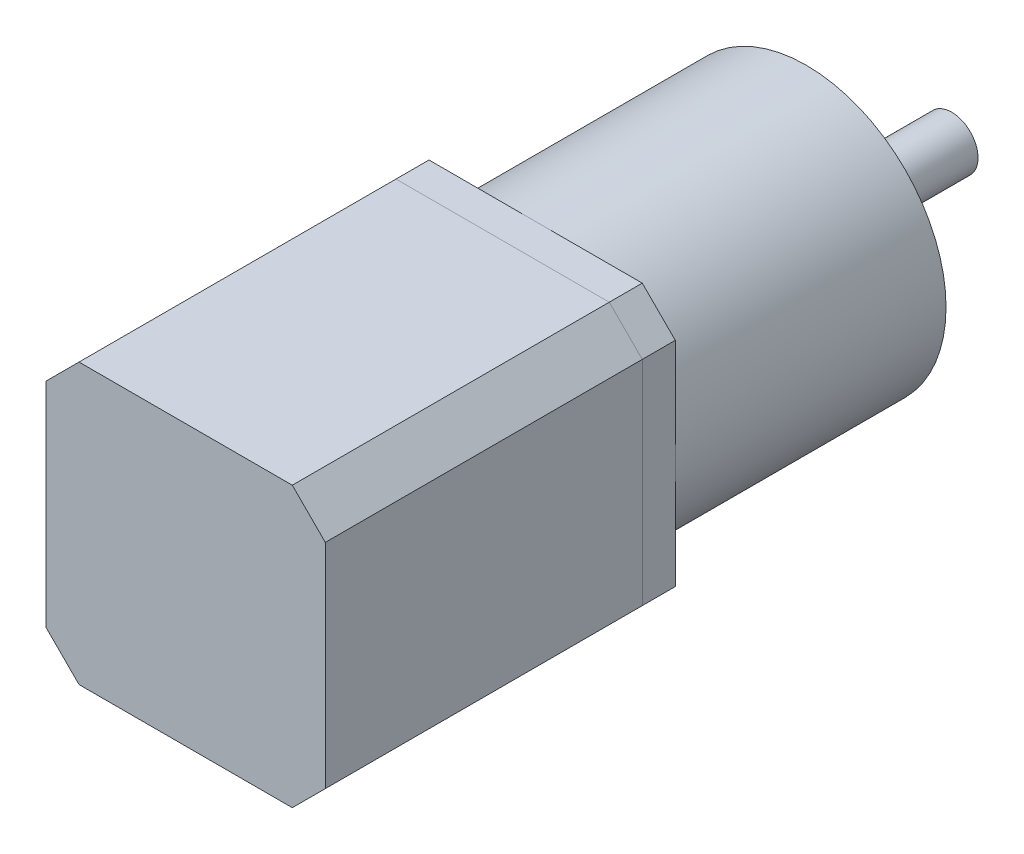
SolidWorks part; units mm, degrees
ref_plane "Front Plane" through (0, 0, 0) normal (0, 0, 1) x (1, 0, 0)
ref_plane "Top Plane" through (0, 0, 0) normal (0, 1, 0) x (1, 0, 0)
ref_plane "Right Plane" through (0, 0, 0) normal (1, 0, 0) x (0, 0, -1)
sketch "Sketch1" plane through (0, 0, 0) normal (0, 0, 1) x (1, 0, 0)
  line L1 (-21.15, 21.15) -> (21.15, 21.15)
  line L2 (-21.15, 21.15) -> (-21.15, -21.15)
  line L3 (-21.15, -21.15) -> (21.15, -21.15)
  line L4 (21.15, 21.15) -> (21.15, -21.15)
  line L5 (-21.15, 21.15) -> (21.15, -21.15) construction
  line L6 (-21.15, -21.15) -> (21.15, 21.15) construction
  point P0 (0, 0)
  dimension "D1" = 42.3
  dimension "D2" = 42.3
extrude "Boss-Extrude1" add sketch "Sketch1" along normal blind 48
chamfer "Chamfer1" distance 5 angle 45 4 edges at (-21.15, -21.15, 24) (21.15, -21.15, 24) (-21.15, 21.15, 24) (21.15, 21.15, 24)
sketch "Sketch2" plane through (0, 0, 0) normal (0, 0, -1) x (-1, 0, 0)
  line L1 (-21.15, -21.15) -> (21.15, -21.15)
  line L2 (-21.15, -21.15) -> (-21.15, 21.15)
  line L3 (-21.15, 21.15) -> (21.15, 21.15)
  line L4 (21.15, -21.15) -> (21.15, 21.15)
  line L5 (-21.15, -21.15) -> (21.15, 21.15) construction
  line L6 (-21.15, 21.15) -> (21.15, -21.15) construction
  point P0 (0, 0)
  dimension "D1" = 42.3
  dimension "D2" = 42.3
extrude "Boss-Extrude2" add sketch "Sketch2" along normal blind 5 separate body
chamfer "Chamfer2" distance 5 angle 45 4 edges at (21.15, -21.15, -2.5) (-21.15, -21.15, -2.5) (21.15, 21.15, -2.5) (-21.15, 21.15, -2.5)
sketch "Sketch3" plane through (0, 0, -5) normal (0, 0, -1) x (-1, 0, 0)
  circle A0 centre (0, 0) radius 21.15
  dimension "D1" = 42.3
extrude "Boss-Extrude3" add sketch "Sketch3" along normal blind 41
sketch "Sketch4" plane through (0, 0, -46) normal (0, 0, -1) x (-1, 0, 0)
  circle A0 centre (0, 0) radius 11
  dimension "D1" = 22
extrude "Boss-Extrude4" add sketch "Sketch4" along normal blind 2
sketch "Sketch5" plane through (0, 0, -48) normal (0, 0, -1) x (-1, 0, 0)
  circle A0 centre (0, 0) radius 4
  dimension "D1" = 8
extrude "Boss-Extrude5" add sketch "Sketch5" along normal blind 20
sketch "Sketch6" plane through (0, 0, -48) normal (0, 0, -1) x (-1, 0, 0)
  circle A0 centre (0, 0) radius 6.211
extrude "Boss-Extrude6" add sketch "Sketch6" along normal blind 0.5
sketch "Sketch7" plane through (0, 0, -46) normal (0, 0, -1) x (-1, 0, 0)
  circle A0 centre (0, 0) radius 17.5 construction
  circle A1 centre (-17.5, 0) radius 1.5
  circle A2 centre (0, 0) radius 17.5 construction
  circle A3 centre (0, 17.5) radius 1.5
  circle A4 centre (0, 0) radius 17.5 construction
  circle A5 centre (17.5, 0) radius 1.5
  circle A6 centre (0, 0) radius 17.5 construction
  circle A7 centre (0, -17.5) radius 1.5
  point P17 (0, 0)
  dimension "D1" = 35
  dimension "D2" = 3
  dimension "D3" = 4
extrude "Cut-Extrude2" cut sketch "Sketch7" against normal blind 10
